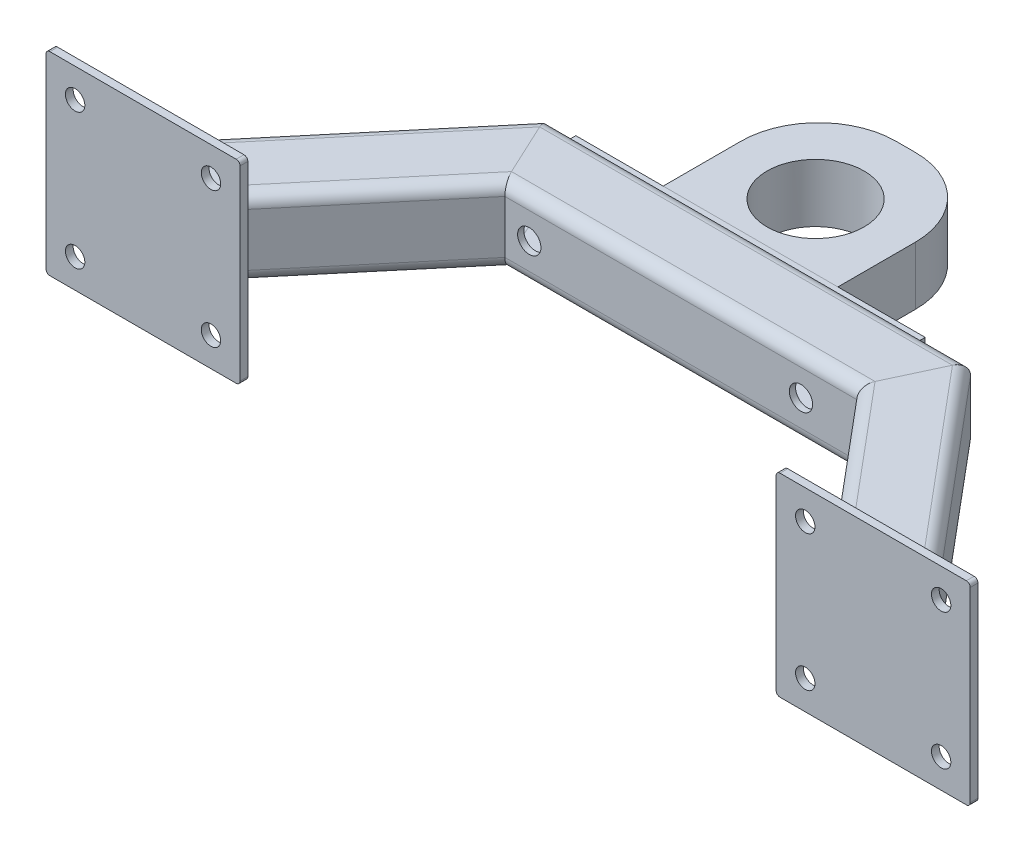
SolidWorks part; units mm, degrees
ref_plane "Front Plane" through (0, 0, 0) normal (0, 0, 1) x (1, 0, 0)
ref_plane "Top Plane" through (0, 0, 0) normal (0, 1, 0) x (1, 0, 0)
ref_plane "Right Plane" through (0, 0, 0) normal (1, 0, 0) x (0, 0, -1)
sketch "Sketch1" plane through (0, 0, 0) normal (0, 1, 0) x (1, 0, 0)
  line L0 (0, 0) -> (96.4965, 115)
  line L1 (96.4965, 115) -> (296.4965, 115)
  line L2 (296.4965, 115) -> (392.9929, 0)
  dimension "D1" = 115
  dimension "D2" = 130
  dimension "D3" = 130
  dimension "D4" = 200
other "Tube (square) 40 X 40 X 3.2(1)"
ref_plane "Plane1" through (0, 0, 0) normal (0.6428, 0, -0.766) x (-0.766, 0, -0.6428)
sketch "Sketch11" plane through (0, 0, 0) normal (0.6428, 0, -0.766) x (-0.766, 0, -0.6428)
  line L0 (-13.6, -16.8) -> (13.6, -16.8)
  line L1 (-16.8, -13.6) -> (-16.8, 13.6)
  line L2 (13.6, 16.8) -> (-13.6, 16.8)
  line L3 (16.8, 13.6) -> (16.8, -13.6)
  line L4 (-13.6, -20) -> (13.6, -20)
  line L5 (-20, -13.6) -> (-20, 13.6)
  line L6 (13.6, 20) -> (-13.6, 20)
  line L7 (20, 13.6) -> (20, -13.6)
  line L8 (-20, 0) -> (-16.8, 0) construction
  line L9 (-16.8, 0) -> (16.8, 0) construction
  line L10 (16.8, 0) -> (20, 0) construction
  line L12 (0, 20) -> (0, 16.8) construction
  line L13 (0, 16.8) -> (0, -16.8) construction
  line L14 (0, -16.8) -> (0, -20) construction
  arc A0 (20, 13.6) -> (13.6, 20) centre (13.6, 13.6) ccw
  arc A1 (13.6, -20) -> (20, -13.6) centre (13.6, -13.6) ccw
  arc A2 (-20, -13.6) -> (-13.6, -20) centre (-13.6, -13.6) ccw
  arc A3 (-13.6, 20) -> (-20, 13.6) centre (-13.6, 13.6) ccw
  arc A4 (-13.6, 16.8) -> (-16.8, 13.6) centre (-13.6, 13.6) ccw
  arc A5 (16.8, 13.6) -> (13.6, 16.8) centre (13.6, 13.6) ccw
  arc A6 (13.6, -16.8) -> (16.8, -13.6) centre (13.6, -13.6) ccw
  arc A7 (-16.8, -13.6) -> (-13.6, -16.8) centre (-13.6, -13.6) ccw
  point P2 (-20, 20)
  point P33 (-20, -20)
  point P34 (20, -20)
  point P36 (20, 20)
  point P37 (0, 0)
  dimension "D1" = 6.4
  dimension "Thickness" = 3.2
  dimension "V_leg" = 40
  dimension "H_leg" = 40
sketch "Sketch13" plane through (0, 0, 0) normal (0, 1, 0) x (1, 0, 0)
  line L0 (0, 0) -> (96.4965, 115) construction
  line L1 (-41.609, 10) -> (58.391, 10)
  line L2 (-41.609, 10) -> (-41.609, 6)
  line L3 (-41.609, 6) -> (58.391, 6)
  line L4 (58.391, 10) -> (58.391, 6)
  line L5 (334.6019, 10) -> (334.6019, 6)
  line L6 (334.6019, 6) -> (434.6019, 6)
  line L7 (434.6019, 10) -> (434.6019, 6)
  line L8 (296.4965, 115) -> (392.9929, 0) construction
  line L10 (334.6019, 10) -> (434.6019, 10)
  point P4 (8.391, 10)
  point P9 (384.6019, 10)
  point P10 (384.6019, 10)
  point P11 (8.391, 10)
  dimension "D1" = 100
  dimension "D2" = 10
  dimension "D3" = 4
  dimension "D4" = 0
  dimension "D5" = 100
  dimension "D6" = 4
  dimension "D7" = 0
extrude "Boss-Extrude1" add sketch "Sketch13" along normal blind 50 and the other way blind 50 separate body
other "Trim/Extend1"
other "Trim/Extend2"
sketch "Sketch14" plane through (0, 0, -135) normal (0, 0, -1) x (-1, 0, 0)
  line L0 (-163.3904, -168.9039) -> (-163.3904, 71.0961) construction
  line L1 (-98.3904, 15) -> (-278.3904, 15)
  line L2 (-98.3904, 15) -> (-98.3904, -15)
  line L3 (-98.3904, -15) -> (-278.3904, -15)
  line L4 (-278.3904, 15) -> (-278.3904, -15)
  line L5 (-98.3904, 15) -> (-278.3904, -15) construction
  line L6 (-98.3904, -15) -> (-278.3904, 15) construction
  line L7 (-302.8382, 20) -> (-90.1547, 20) construction
  point P0 (-188.3904, 0)
  dimension "D1" = 180
  dimension "D2" = 30
  dimension "D3" = 25
  dimension "D4" = 5
extrude "Boss-Extrude2" add sketch "Sketch14" along normal blind 4 separate body
sketch "Sketch15" plane through (0, 0, -139) normal (0, 0, -1) x (-1, 0, 0)
  line L0 (-98.3904, 15) -> (-278.3904, 15) construction
  line L1 (-143.3904, -15) -> (-233.3904, -15)
  line L2 (-143.3904, -15) -> (-143.3904, 15)
  line L3 (-143.3904, 15) -> (-233.3904, 15)
  line L4 (-233.3904, -15) -> (-233.3904, 15)
  line L5 (-143.3904, -15) -> (-233.3904, 15) construction
  line L6 (-143.3904, 15) -> (-233.3904, -15) construction
  line L7 (-213.3904, 71.0961) -> (-213.3904, -168.9039) construction
  line L8 (-163.3904, -168.9039) -> (-163.3904, 71.0961) construction
  point P0 (-188.3904, 0)
  dimension "D1" = 20
  dimension "D2" = 20
extrude "Boss-Extrude3" add sketch "Sketch15" along normal blind 80 separate body
fillet "Fillet1" radius 40 1 edges at (233.3904, 0, -219)
fillet "Fillet2" radius 40 1 edges at (143.3904, 0, -219)
sketch "Sketch16" plane through (0, -15, 0) normal (0, -1, 0) x (1, 0, 0)
  circle A0 centre (188.3904, -172.516) radius 25 construction
  circle A1 centre (188.3904, -172.516) radius 25
extrude "Cut-Extrude1" cut sketch "Sketch16" against normal up to next (30 mm away)
sketch "Sketch17" plane through (0, 0, -139) normal (0, 0, -1) x (-1, 0, 0)
  line L0 (-278.3904, 15) -> (-278.3904, -15) construction
  line L1 (-98.3904, -15) -> (-98.3904, 15) construction
  circle A0 centre (-258.3904, 0) radius 6
  circle A1 centre (-118.3904, 0) radius 6
  dimension "D1" = 12
  dimension "D2" = 12
  dimension "D3" = 20
  dimension "D4" = 20
extrude "Cut-Extrude2" cut sketch "Sketch17" against normal through all
sketch "Sketch18" plane through (0, 0, -6) normal (0, 0, 1) x (1, 0, 0)
  line L0 (334.6019, -50) -> (334.6019, 50) construction
  line L1 (334.6019, -50) -> (434.6019, -50) construction
  circle A0 centre (349.6019, -35) radius 5
  circle A1 centre (419.6019, -35) radius 5
  circle A2 centre (419.6019, 35) radius 5
  circle A3 centre (349.6019, 35) radius 5
  circle A4 centre (43.391, 35) radius 5
  circle A5 centre (43.391, -35) radius 5
  circle A6 centre (-26.609, -35) radius 5
  circle A7 centre (-26.609, 35) radius 5
  dimension "D1" = 10
  dimension "D6" = 10
  dimension "D2" = 15
  dimension "D3" = 15
  dimension "D4" = 2
  dimension "D5" = 2
extrude "Cut-Extrude3" cut sketch "Sketch18" against normal up to next (4 mm away)
fillet "Fillet3" radius 2 4 edges at (334.6019, 50, -8) (334.6019, -50, -8) (434.6019, -50, -8) (434.6019, 50, -8)
fillet "Fillet4" radius 2 3 edges at (58.391, 50, -8) (58.391, -50, -8) (-41.609, -50, -8)
fillet "Fillet5" radius 2 1 edges at (-41.609, 50, -8)
